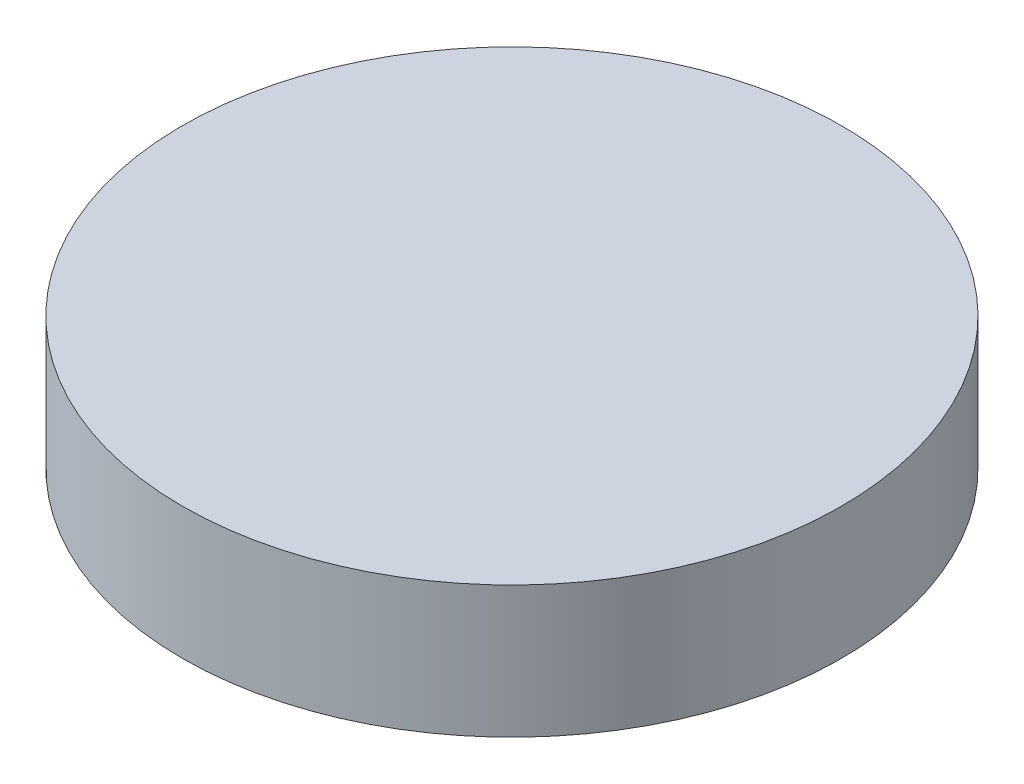
SolidWorks part; units mm, degrees
material "ABS"
ref_plane "Front Plane" through (0, 0, 0) normal (0, 0, 1) x (1, 0, 0)
ref_plane "Top Plane" through (0, 0, 0) normal (0, 1, 0) x (1, 0, 0)
ref_plane "Right Plane" through (0, 0, 0) normal (1, 0, 0) x (0, 0, -1)
sketch "Sketch1" plane through (0, 0, 0) normal (0, 1, 0) x (1, 0, 0)
  circle A0 centre (0, 0) radius 6.35
extrude "Boss-Extrude1" add sketch "Sketch1" along normal blind 2.54 contours A0
